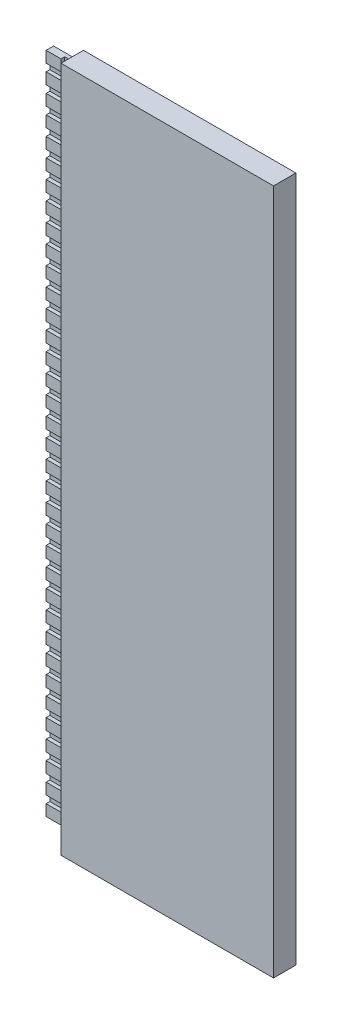
SolidWorks part; units mm, degrees
ref_plane "Plane1" through (0, 0, 0) normal (0, 0, 1) x (1, 0, 0)
ref_plane "Plane2" through (0, 0, 0) normal (0, 1, 0) x (1, 0, 0)
ref_plane "Plane3" through (0, 0, 0) normal (1, 0, 0) x (0, 0, -1)
sketch "Sketch1" plane through (0, 0, 0) normal (0, 0, 1) x (1, 0, 0)
  line L0 (1.425, 4.6) -> (-1.425, 4.6)
  line L1 (-1.425, 4.6) -> (-1.425, -4.6)
  line L2 (-1.425, -4.6) -> (1.425, -4.6)
  line L3 (1.425, -4.6) -> (1.425, 4.6)
  line L4 (-1.425, 4.6) -> (1.425, -4.6) construction
  dimension "D1" = 2.85
  dimension "D2" = 9.2
extrude "Extrude1" add sketch "Sketch1" along normal blind 0.3
sketch "Sketch2" plane through (0, 0, 0) normal (0, 0, 1) x (1, 0, 0)
  line L0 (-1.425, 4.6) -> (-1.425, -4.6) construction
  line L1 (-1.425, 4.45) -> (-1.825, 4.45)
  line L2 (-1.425, 4.45) -> (-1.425, -4.45)
  line L3 (-1.425, -4.45) -> (-1.825, -4.45)
  line L4 (-1.825, 4.45) -> (-1.825, -4.45)
  line L5 (1.425, 4.6) -> (-1.425, 4.6) construction
  line L6 (-1.425, -4.6) -> (1.425, -4.6) construction
  dimension "D1" = 0.4
  dimension "D2" = 0.15
  dimension "D3" = 0.15
extrude "Extrude2" add sketch "Sketch2" along normal blind 0.05
sketch "Sketch3" plane through (0, 0, 0.05) normal (0, 0, 1) x (1, 0, 0)
  line L0 (-1.825, -4.45) -> (-1.425, -4.45) construction
  line L1 (-1.825, 4.45) -> (-1.625, 4.45)
  line L2 (-1.825, 4.45) -> (-1.825, -4.45)
  line L3 (-1.825, -4.45) -> (-1.625, -4.45)
  line L4 (-1.625, 4.45) -> (-1.625, -4.45)
  dimension "D1" = 0.2
extrude "Extrude3" add sketch "Sketch3" along normal blind 0.05
sketch "Sketch4" plane through (0, 0, 0.05) normal (0, 0, 1) x (1, 0, 0)
  line L0 (-1.625, -4.45) -> (-1.625, 4.45) construction
  line L1 (-1.625, -4.3) -> (-1.825, -4.3)
  line L2 (-1.625, -4.3) -> (-1.625, -4.2)
  line L3 (-1.625, -4.2) -> (-1.825, -4.2)
  line L4 (-1.825, -4.3) -> (-1.825, -4.2)
  line L5 (-1.825, 4.45) -> (-1.825, -4.45) construction
  line L6 (-1.825, -4.45) -> (-1.625, -4.45) construction
  dimension "D1" = 0.1
  dimension "D2" = 0.15
extrude "Extrude4" cut sketch "Sketch4" along normal through all
pattern_linear "LPattern1" count 35 spacing 0.25 along (0, 1, 0) of "Extrude4"
